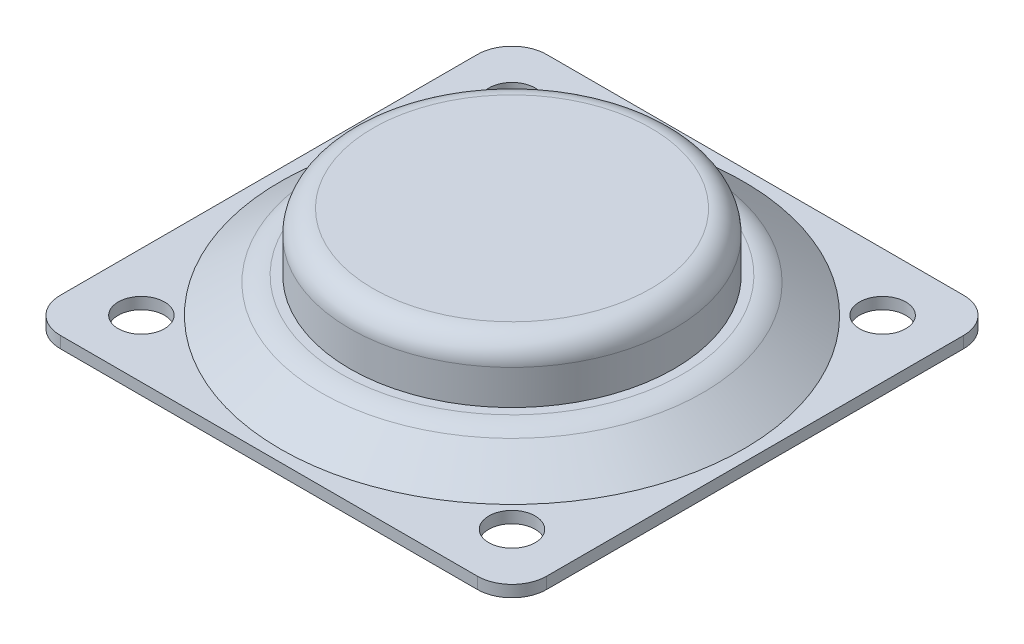
SolidWorks part; units mm, degrees
material "AISI 304"
ref_plane "Plan de face" through (0, 0, 0) normal (0, 0, 1) x (1, 0, 0)
ref_plane "Plan de dessus" through (0, 0, 0) normal (0, 1, 0) x (1, 0, 0)
ref_plane "Plan de droite" through (0, 0, 0) normal (1, 0, 0) x (0, 0, -1)
sketch "Esquisse1" plane through (0, 0, 0) normal (0, 1, 0) x (1, 0, 0)
  line L0 (0, 21) -> (0, -21) construction
  line L1 (-21, -21) -> (21, -21)
  line L2 (-21, -21) -> (-21, 21)
  line L3 (-21, 21) -> (21, 21)
  line L4 (21, -21) -> (21, 21)
  line L5 (21, 0) -> (-21, 0) construction
  dimension "D1" = 42
  dimension "D2" = 42
extrude "Boss.-Extru.1" add sketch "Esquisse1" along normal blind 1
fillet "Congé1" radius 3 4 edges at (-21, 0.5, -21) (21, 0.5, -21) (21, 0.5, 21) (-21, 0.5, 21)
sketch "Esquisse2" plane through (0, 0, 0) normal (1, 0, 0) x (0, 0, -1)
  line L1 (-20, 1) -> (-16.4904, 3.4575)
  line L2 (-18, 1) -> (18, 1) construction
  line L4 (0, 4) -> (0, 1)
  line L5 (0, 1) -> (-20, 1)
  line L6 (-14.7697, 4) -> (-14, 4)
  line L7 (-14, 4) -> (-14, 7)
  line L8 (-12, 9) -> (0, 9)
  line L9 (0, 9) -> (0, 4)
  arc A0 (-16.4904, 3.4575) -> (-14.7697, 4) centre (-14.7697, 1) cw
  arc A1 (-14, 7) -> (-12, 9) centre (-12, 7) cw
  dimension "D6" = 2
  dimension "D1" = 3
  dimension "D2" = 35
  dimension "D3" = 20
  dimension "D4" = 14
  dimension "D5" = 5
revolve "Révolution1" add sketch "Esquisse2" angle 360 about L4
sketch "Esquisse3" plane through (0, 0, 0) normal (0, -1, 0) x (1, 0, 0)
  line L0 (-18, 21) -> (18, 21) construction
  line L1 (-21, -18) -> (-21, 18) construction
  line L2 (-21, 0) -> (21, 0) construction
  line L3 (21, 18) -> (21, -18) construction
  line L4 (0, 21) -> (0, -21) construction
  line L5 (18, -21) -> (-18, -21) construction
  circle A0 centre (-16, 16) radius 2
  circle A1 centre (16, 16) radius 2
  circle A2 centre (-16, -16) radius 2
  circle A3 centre (16, -16) radius 2
  dimension "D3" = 4
  dimension "D1" = 5
  dimension "D2" = 5
extrude "Enlèv. mat.-Extru.1" cut sketch "Esquisse3" against normal up to next
